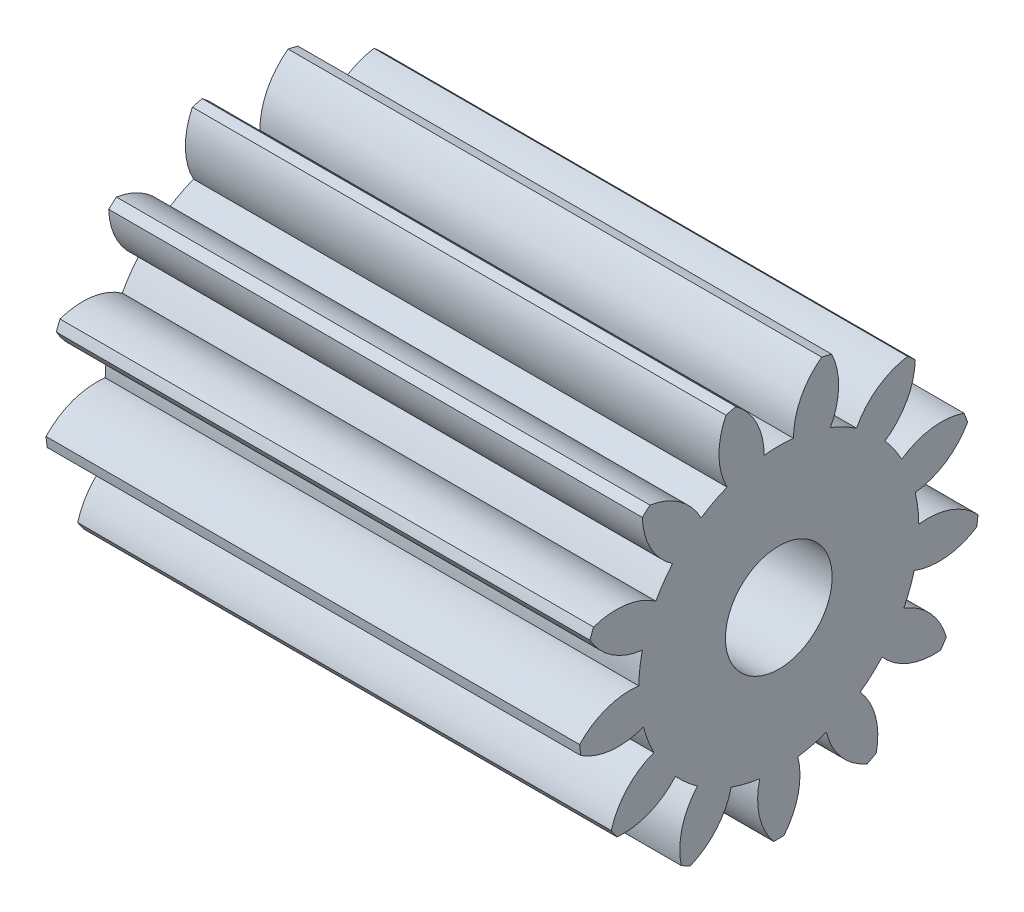
SolidWorks part; units mm, degrees
material "1.0035 (S185)"
ref_plane "Plane1" through (0, 0, 0) normal (0, 0, 1) x (1, 0, 0)
ref_plane "Plane2" through (0, 0, 0) normal (0, 1, 0) x (1, 0, 0)
ref_plane "Plane3" through (0, 0, 0) normal (1, 0, 0) x (0, 0, -1)
sketch "HoldingSke" plane through (0, 0, 0) normal (0, 1, 0) x (1, 0, 0)
  line L0 (0, 0) -> (1.9487, -0.4499)
  line L1 (-15, 0) -> (100, 0) construction
  line L2 (0, 0) -> (-2.1039, 2.3779)
  line L3 (0, 0) -> (-11.863, 4.5341)
  line L4 (0, 0) -> (8.4147, 1.9427)
  line L5 (0, 0) -> (-46.8476, -17.4728)
  line L6 (0, 0) -> (-8.2896, -5.593)
  line L7 (-2.1039, 2.3779) -> (8.6586, 51.2059)
  line L8 (-76.2, 54.61) -> (-75.9, 54.61)
  line L9 (-71.009, 38.7566) -> (-53.1078, 45.2721)
  line L10 (-76.2, 71.12) -> (104.1128, 71.12)
  line L11 (0, 0) -> (-10, 0)
  line L12 (-76.2, 101.6) -> (-76.181, 101.6)
  line L13 (24.9733, 27.94) -> (52.9518, 28.4284)
  line L14 (24.9733, 27.94) -> (24.9743, 27.94)
  line L15 (24.9733, 27.94) -> (100.4006, 29.5858)
  line L16 (-63.627, -0.5) -> (-12.827, -0.5)
  circle A0 centre (0, 0) radius 1
  circle A1 centre (0, 0) radius 2.624
  circle A2 centre (0, 0) radius 37.5
  circle A3 centre (0, 0) radius 1
  dimension "MHD" = 5.248
  dimension "Hub_dia" = 75
  dimension "Bore" = 2
  dimension "MBD" = 2
  dimension "Num_teeth" = 13
  dimension "Pitch_radius" = 180.3128
  dimension "Pitch" = 2
  dimension "Width" = 10
  dimension "Overall_len" = 50
  dimension "Show_teeth" = 13
  dimension "Thickness" = 10
  dimension "OAL" = 50.0001
  dimension "T_dim" = 0.3
  dimension "Ap" = 20
  dimension "H" = 19.05
  dimension "Backlash" = 0.019
  dimension "Addendum_fac" = 1
  dimension "Dedendum_fac" = 1.25
  dimension "Clearance_fac" = 0.25
  dimension "Dedendum_add" = 0.001
  dimension "Module" = 0.5
sketch "BasProSke" plane through (0, 0, 0) normal (0, 1, 0) x (1, 0, 0)
  line L0 (-10, 0) -> (60, 0) construction
  line L1 (0, 0) -> (0, 3.75)
  line L2 (0, 0) -> (10, 0)
  line L3 (10, 0) -> (10, 3.75)
  line L4 (10, 3.75) -> (0, 3.75)
  dimension "Diameter" = 7.5
  dimension "Thickness" = 10
revolve "Base-Revolve" add sketch "BasProSke" angle 360 about L0
sketch "TooCutSke" plane through (0, 0, 0) normal (1, 0, 0) x (0, 0, -1)
  line L1 (0, 0) -> (0, 107) construction
  line L2 (0, 0) -> (-0.425, 3.2221) construction
  line L3 (0, 0) -> (-1.5461, 6.2726) construction
  line L4 (-0.425, 3.2221) -> (-0.773, 3.1363) construction
  arc A0 (0.2752, 2.6095) -> (-0.2752, 2.6095) centre (0, 0) ccw
  arc A1 (0.8316, 3.6827) -> (-0.8316, 3.6827) centre (0, 0) ccw
  circle A2 centre (0, 0) radius 3.25 construction
  circle A3 centre (0, 0) radius 3.054 construction
  arc A4 (-0.2752, 2.6095) -> (-0.8316, 3.6827) centre (-1.5752, 2.6164) ccw
  arc A5 (0.8316, 3.6827) -> (0.2752, 2.6095) centre (1.5752, 2.6164) ccw
  dimension "Root_dia" = 5.248
  dimension "Overcut_dia" = 7.5508
  dimension "Pitch_dia" = 6.5
  dimension "Base_dia" = 6.108
  dimension "Flank_rad" = 1.3
  dimension "Half_ang" = 13.846
  dimension "Half_CT" = 0.3585
extrude "ToothCut" cut sketch "TooCutSke" along normal through all
fillet "Breaks" [suppressed] radius 0.01
fillet "RootFillets" [suppressed] radius 0.126
pattern_circular "TeethCuts" count 13 every 27.692 about axis through (-10, 0, 0) along (1, 0, 0) of "ToothCut", "RootFillets", "Breaks"
sketch "HubNeaOneSke" plane through (0, 0, 0) normal (-1, 0, 0) x (0, 0, 1)
  circle A0 centre (0, 0) radius 2.624
  dimension "Diameter" = 5.248
extrude "HubNearOne" [suppressed] add sketch "HubNeaOneSke" along normal blind 40.0001
sketch "HubNeaBotSke" plane through (0, 0, 0) normal (-1, 0, 0) x (0, 0, 1)
  circle A0 centre (0, 0) radius 2.624
  dimension "Diameter" = 5.248
extrude "HubNearBoth" [suppressed] add sketch "HubNeaBotSke" along normal blind 20
ref_plane "FarPln" through (10, 0, 0) normal (1, 0, 0) x (0, 0, -1)
sketch "HubFarSke" plane through (10, 0, 0) normal (1, 0, 0) x (0, 0, -1)
  circle A0 centre (0, 0) radius 2.624
  dimension "Diameter" = 5.248
extrude "HubFar" [suppressed] add sketch "HubFarSke" along normal blind 20
sketch "BorSke" plane through (0, 0, 0) normal (1, 0, 0) x (0, 0, -1)
  circle A0 centre (0, 0) radius 1
  dimension "Diameter" = 2
extrude "Bore" cut sketch "BorSke" along normal mid plane 100.0001
sketch "KeySke" plane through (0, 0, 0) normal (1, 0, 0) x (0, 0, -1)
  line L0 (-0.4, 0) -> (-0.4, 1.3)
  line L1 (-0.4, 1.3) -> (0.4, 1.3)
  line L2 (0.4, 1.3) -> (0.4, 0)
  line L3 (0, 0) -> (0, 34) construction
  line L4 (-0.4, 0) -> (0.4, 0)
  dimension "Offset" = 1.3
  dimension "Width" = 0.8
extrude "Keyway" [suppressed] cut sketch "KeySke" along normal mid plane 100.0001
pattern_circular "Keyway2" [suppressed] count 2 every 90 about axis through (-10, 0, 0) along (1, 0, 0)
equation "' \"Module@HoldingSke\" = 6.35"
equation "' \"Num_teeth@HoldingSke\" = 12"
equation "' \"Ap@HoldingSke\" =  20"
equation "' \"Width@HoldingSke\" = 0.5 * 25.4"
equation "' \"Hub_dia@HoldingSke\"= 1 * 25.4"
equation "' \"Overall_len@HoldingSke\" = 1.0 * 25.4"
equation "' \"Bore@HoldingSke\" = 0.75 * 25.4"
equation "' \"T_dim@HoldingSke\" = 0.1 * 25.4"
equation "' \"Width@KeySke\" = 0.25 * 25.4"
equation "' \"Show_teeth@HoldingSke\" = 13"
equation "' \"Backlash@HoldingSke\" = 0.009 * 25.4"
equation "' \"Addendum_fac@HoldingSke\" = 1.0"
equation "' \"Dedendum_fac@HoldingSke\" = 1.25"
equation "' \"Dedendum_add@HoldingSke\" = 0.00005 * 25.4"
equation "' \"Clearance_fac@HoldingSke\" = 0.25"
equation "\"Pitch@HoldingSke\" = 1 / \"Module@HoldingSke\""
equation "\"Overcut_dia@TooCutSke\" = (\"Num_teeth@HoldingSke\" + 2 * \"Addendum_fac@HoldingSke\") / \"Pitch@HoldingSke\" + 0.002 * 25.4"
equation "\"Pitch_dia@TooCutSke\" = \"Num_teeth@HoldingSke\" / \"Pitch@HoldingSke\""
equation "\"Base_dia@TooCutSke\" = \"Num_teeth@HoldingSke\" / \"Pitch@HoldingSke\" * cos((\"Ap@HoldingSke\"  * 3.14159265 / 180))"
equation "\"Root_dia@TooCutSke\" = (\"Num_teeth@HoldingSke\" + 2) / \"Pitch@HoldingSke\" - 2 * (\"Addendum_fac@HoldingSke\" + \"Dedendum_fac@HoldingSke\") / \"Pitch@HoldingSke\" - \"Dedendum_add@HoldingSke\" * 2"
equation "\"Half_ang@TooCutSke\" = 180 / \"Num_teeth@HoldingSke\""
equation "\"Half_CT@TooCutSke\" = \"Num_teeth@HoldingSke\" / \"Pitch@HoldingSke\" * sin((3.14159265 / 2 / \"Num_teeth@HoldingSke\")) / 2 - 7 * \"Backlash@HoldingSke\" / 4"
equation "\"Flank_rad@TooCutSke\" = \"Num_teeth@HoldingSke\" / \"Pitch@HoldingSke\" / 5"
equation "\"Radius@RootFillets\" = \"Clearance_fac@HoldingSke\" / \"Pitch@HoldingSke\" + \"Dedendum_add@HoldingSke\""
equation "\"Break_rad@Breaks\" = 0.02 / \"Pitch@HoldingSke\""
equation "\"Thickness@HoldingSke\" = \"Width@HoldingSke\""
equation "\"OAL@HoldingSke\" = \"Thickness@HoldingSke\""
equation "\"MHD@HoldingSke\" = (\"Num_teeth@HoldingSke\" + 2) / \"Pitch@HoldingSke\" - 2 * (\"Addendum_fac@HoldingSke\" + \"Dedendum_fac@HoldingSke\")  / \"Pitch@HoldingSke\" - \"Dedendum_add@HoldingSke\" * 2"
equation "\"MBD@HoldingSke\" = (\"Num_teeth@HoldingSke\" + 2) / \"Pitch@HoldingSke\" - 2 * (\"Addendum_fac@HoldingSke\" + \"Dedendum_fac@HoldingSke\")  / \"Pitch@HoldingSke\" - \"Dedendum_add@HoldingSke\" * 2 - 0.002 * 25.4"
equation "\"MHD@HoldingSke\" = ((sgn( \"MHD@HoldingSke\" - \"Hub_dia@HoldingSke\" )-1)*( \"MHD@HoldingSke\" - \"Hub_dia@HoldingSke\" ))/-2+ \"Hub_dia@HoldingSke\""
equation "\"MBD@HoldingSke\" = ((sgn( \"MBD@HoldingSke\" - \"Bore@HoldingSke\" )-1)*( \"MBD@HoldingSke\" - \"Bore@HoldingSke\" ))/-2+ \"Bore@HoldingSke\""
equation "\"OAL@HoldingSke\" = ((sgn( \"OAL@HoldingSke\" - \"Overall_len@HoldingSke\" )+1)*( \"OAL@HoldingSke\" - \"Overall_len@HoldingSke\" ))/2 + \"Overall_len@HoldingSke\" + 0.000002 * 25.4"
equation "\"Num_teeth@TeethCuts\" = int( \"Show_teeth@HoldingSke\" ) + 1"
equation "\"Num_teeth@TeethCuts\" = ((sgn( \"Num_teeth@TeethCuts\" - \"Num_teeth@HoldingSke\" )-1)*( \"Num_teeth@TeethCuts\" - \"Num_teeth@HoldingSke\" ))/-2+ \"Num_teeth@HoldingSke\""
equation "\"Num_teeth@TeethCuts\" = ((sgn( \"Num_teeth@TeethCuts\" - 2.0)+1)*( \"Num_teeth@TeethCuts\" - 2.0))/2 +2.0"
equation "\"Angle@TeethCuts\" = 360.0 / \"Num_teeth@HoldingSke\""
equation "\"Diameter@BasProSke\" = (\"Num_teeth@HoldingSke\" + 2 * \"Addendum_fac@HoldingSke\") / \"Pitch@HoldingSke\""
equation "\"Thickness@BasProSke\"  = \"Thickness@HoldingSke\""
equation "' \"Fillet_rad@BasProSke\" =  \"Thickness@HoldingSke\" * 0.05"
equation "\"MHD@HoldingSke\" = ((sgn( \"MHD@HoldingSke\" - \"Root_dia@TooCutSke\" )-1)*( \"MHD@HoldingSke\" - \"Root_dia@TooCutSke\" ))/-2+ \"Root_dia@TooCutSke\""
equation "\"Diameter@HubNeaOneSke\" = \"MHD@HoldingSke\""
equation "\"Length@HubNearOne\" = \"OAL@HoldingSke\" - \"Thickness@BasProSke\""
equation "\"Diameter@HubNeaBotSke\" = \"MHD@HoldingSke\""
equation "\"Length@HubNearBoth\" = ( \"OAL@HoldingSke\" - \"Thickness@BasProSke\" ) / 2.0"
equation "\"Thickness@FarPln\" = \"Thickness@BasProSke\""
equation "\"Diameter@HubFarSke\" = \"MHD@HoldingSke\""
equation "\"Length@HubFar\" = ( \"OAL@HoldingSke\" - \"Thickness@BasProSke\" ) / 2.0"
equation "\"Diameter@BorSke\" = \"MBD@HoldingSke\""
equation "\"D1@Bore\" = \"OAL@HoldingSke\" * 2.0"
equation "\"D1@Keyway\" = \"OAL@HoldingSke\" * 2.0"
equation "\"Offset@KeySke\" = \"T_dim@HoldingSke\" + \"MBD@HoldingSke\" / 2.0"
